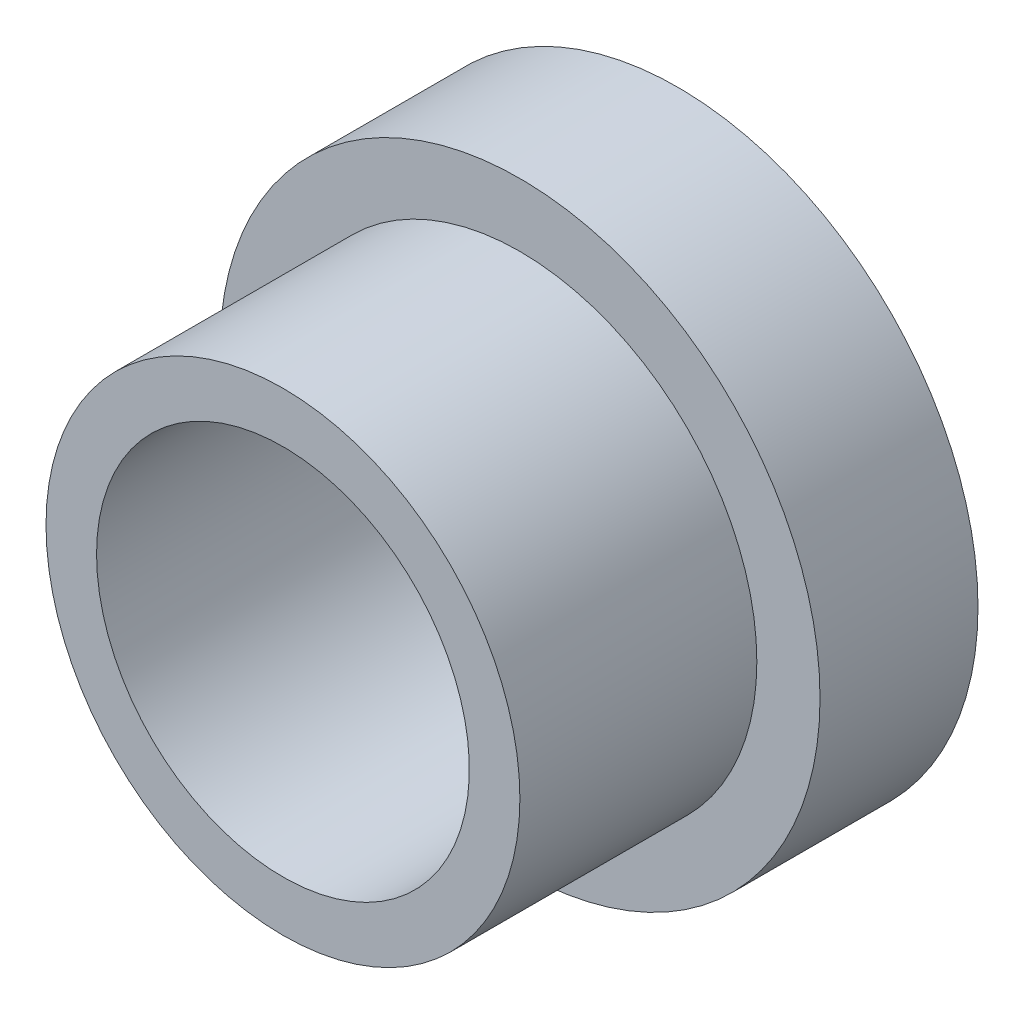
SolidWorks part; units mm, degrees
ref_plane "Front Plane" through (0, 0, 0) normal (0, 0, 1) x (1, 0, 0)
ref_plane "Top Plane" through (0, 0, 0) normal (0, 1, 0) x (1, 0, 0)
ref_plane "Right Plane" through (0, 0, 0) normal (1, 0, 0) x (0, 0, -1)
sketch "Sketch1" plane through (0, 0, 0) normal (0, 0, 1) x (1, 0, 0)
  circle A0 centre (0, 0) radius 12.065
  dimension "D1" = 24.13
extrude "Boss-Extrude1" add sketch "Sketch1" along normal blind 6.35
sketch "Sketch2" plane through (0, 0, 6.35) normal (0, 0, 1) x (1, 0, 0)
  circle A0 centre (0, 0) radius 9.525
  dimension "D1" = 19.05
extrude "Boss-Extrude2" add sketch "Sketch2" along normal blind 9.525
sketch "Sketch3" plane through (0, 0, 0) normal (0, 0, -1) x (-1, 0, 0)
  circle A0 centre (0, 0) radius 7.493
  dimension "D1" = 14.986
extrude "Cut-Extrude1" cut sketch "Sketch3" against normal through all
sketch "Sketch4" plane through (0, 0, 0) normal (1, 0, 0) x (0, 0, -1)
  line L0 (-3.175, 12.065) -> (-3.175, -12.065) construction
  line L1 (0, 12.065) -> (-6.35, 12.065) construction
  line L2 (-6.35, -12.065) -> (0, -12.065) construction
  circle A0 centre (-3.175, 0) radius 1.7272
  dimension "D1" = 3.4544
extrude "Cut-Extrude2" cut sketch "Sketch4" against normal through all
